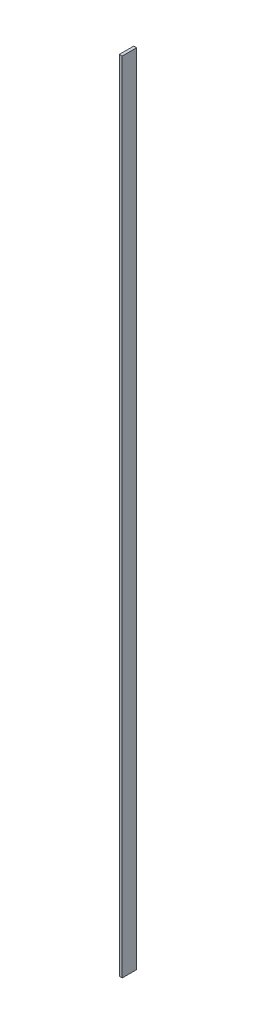
SolidWorks part; units mm, degrees
ref_plane "Спереди" through (0, 0, 0) normal (0, 0, 1) x (1, 0, 0)
ref_plane "Сверху" through (0, 0, 0) normal (0, 1, 0) x (1, 0, 0)
ref_plane "Справа" through (0, 0, 0) normal (1, 0, 0) x (0, 0, -1)
sketch "Эскиз1" plane through (0, 0, 0) normal (0, 1, 0) x (1, 0, 0)
  line L1 (-2, 10) -> (2, 10)
  line L2 (-2, 10) -> (-2, -10)
  line L3 (-2, -10) -> (2, -10)
  line L4 (2, 10) -> (2, -10)
  line L5 (-2, 10) -> (2, -10) construction
  line L6 (-2, -10) -> (2, 10) construction
  point P0 (0, 0)
extrude "Бобышка-Вытянуть1" add sketch "Эскиз1" along normal blind 1100
